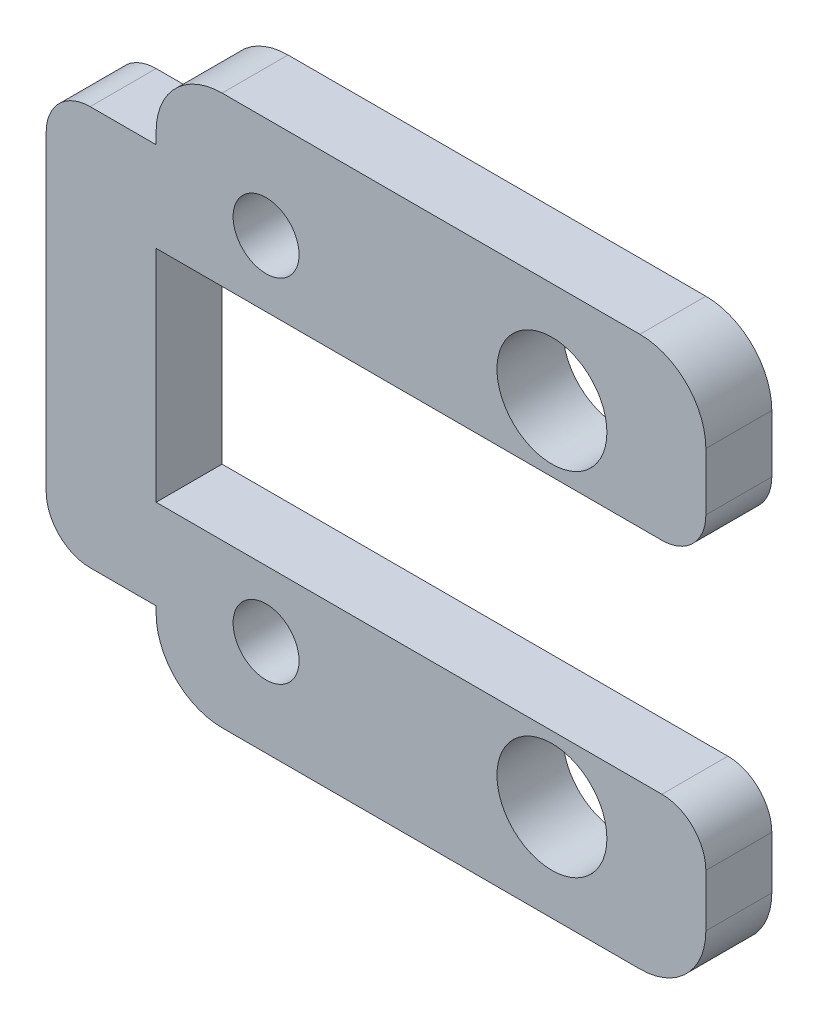
SolidWorks part; units mm, degrees
ref_plane "Front Plane" through (0, 0, 0) normal (0, 0, 1) x (1, 0, 0)
ref_plane "Top Plane" through (0, 0, 0) normal (0, 1, 0) x (1, 0, 0)
ref_plane "Right Plane" through (0, 0, 0) normal (1, 0, 0) x (0, 0, -1)
sketch "Sketch1" plane through (0, 0, 0) normal (0, 0, 1) x (1, 0, 0)
  line L0 (-47.8824, -2.6156) -> (-50.3824, -2.6156)
  line L1 (-55.3824, 7.3844) -> (-50.3824, 7.3844)
  line L2 (-50.3824, -2.6156) -> (-55.3824, -2.6156)
  line L12 (-67.8824, 15) -> (-48.8824, 15)
  line L13 (-45.8824, 12) -> (-45.8824, 9.3844)
  line L27 (-47.8824, 7.3844) -> (-50.3824, 7.3844)
  line L31 (-45.8824, -4.6156) -> (-45.8824, -7)
  line L32 (-48.8824, -10) -> (-67.8824, -10)
  line L33 (-70.8824, -7) -> (-70.8824, -6.6968)
  line L34 (-70.8824, -6.6968) -> (-73.8824, -6.6968)
  line L35 (-75.8824, -4.6968) -> (-75.8824, 9.4656)
  line L36 (-73.8824, 11.4656) -> (-70.8824, 11.4656)
  line L37 (-70.8824, 11.4656) -> (-70.8824, 12)
  line L40 (-55.3824, -2.6156) -> (-70.8824, -2.6156)
  line L41 (-70.8824, -2.6156) -> (-70.8824, 7.3844)
  line L42 (-70.8824, 7.3844) -> (-55.3824, 7.3844)
  line L44 (-70.8824, 2.3844) -> (-41.4465, 2.3844) construction
  arc A0 (-73.8824, -6.6968) -> (-75.8824, -4.6968) centre (-73.8824, -4.6968) cw
  arc A1 (-75.8824, 9.4656) -> (-73.8824, 11.4656) centre (-73.8824, 9.4656) cw
  circle A3 centre (-52.8824, 10.3844) radius 2.5
  circle A4 centre (-52.8824, -5.6156) radius 2.5
  circle A13 centre (-65.8824, 10.3844) radius 1.5
  circle A14 centre (-65.8824, -5.6156) radius 1.5
  arc A15 (-70.8824, 12) -> (-67.8824, 15) centre (-67.8824, 12) cw
  arc A16 (-70.8824, -7) -> (-67.8824, -10) centre (-67.8824, -7) ccw
  arc A17 (-48.8824, -10) -> (-45.8824, -7) centre (-48.8824, -7) ccw
  arc A18 (-45.8824, 9.3844) -> (-47.8824, 7.3844) centre (-47.8824, 9.3844) cw
  arc A19 (-45.8824, -4.6156) -> (-47.8824, -2.6156) centre (-47.8824, -4.6156) ccw
  arc A20 (-45.8824, 12) -> (-48.8824, 15) centre (-48.8824, 12) ccw
  point P86 (-45.8824, 7.3844)
  dimension "D3" = 2
  dimension "D5" = 3
  dimension "D6" = 5
  dimension "D7" = 7
  dimension "D13" = 3
  dimension "D12" = 2
  dimension "D22" = 3
  dimension "D18" = 25
  dimension "D20" = 25
extrude "Boss-Extrude1" add sketch "Sketch1" along normal blind 3
